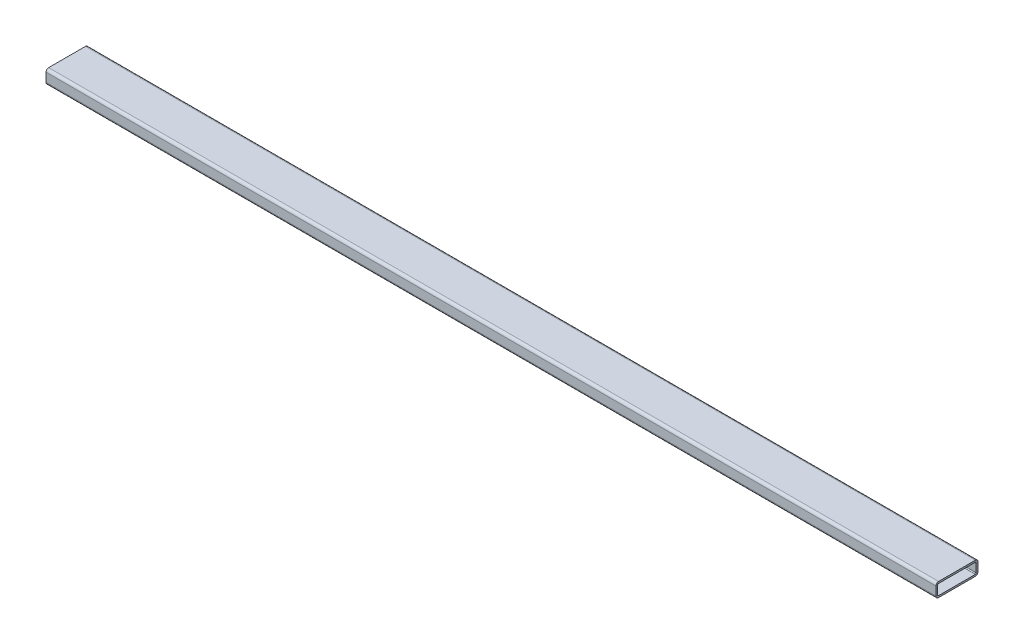
SolidWorks part; units mm, degrees
ref_plane "Front Plane" through (0, 0, 0) normal (0, 0, 1) x (1, 0, 0)
ref_plane "Top Plane" through (0, 0, 0) normal (0, 1, 0) x (1, 0, 0)
ref_plane "Right Plane" through (0, 0, 0) normal (1, 0, 0) x (0, 0, -1)
sketch "Sketch1" plane through (0, 0, 0) normal (1, 0, 0) x (0, 0, -1)
  line L0 (33.3248, 22.225) -> (-33.3248, 22.225)
  line L1 (33.3248, 25.4) -> (-33.3248, 25.4)
  line L2 (38.1, 20.6248) -> (38.1, 4.7752)
  line L3 (33.3248, 0) -> (-33.3248, 0)
  line L4 (-38.1, 20.6248) -> (-38.1, 4.7752)
  line L5 (-34.925, 20.6248) -> (-34.925, 4.7752)
  line L6 (33.3248, 3.175) -> (-33.3248, 3.175)
  line L7 (34.925, 20.6248) -> (34.925, 4.7752)
  arc A0 (38.1, 20.6248) -> (33.3248, 25.4) centre (33.3248, 20.6248) ccw
  arc A1 (38.1, 4.7752) -> (33.3248, 0) centre (33.3248, 4.7752) cw
  arc A2 (-33.3248, 0) -> (-38.1, 4.7752) centre (-33.3248, 4.7752) cw
  arc A3 (-38.1, 20.6248) -> (-33.3248, 25.4) centre (-33.3248, 20.6248) cw
  arc A4 (-34.925, 20.6248) -> (-33.3248, 22.225) centre (-33.3248, 20.6248) cw
  arc A5 (-33.3248, 3.175) -> (-34.925, 4.7752) centre (-33.3248, 4.7752) cw
  arc A6 (34.925, 4.7752) -> (33.3248, 3.175) centre (33.3248, 4.7752) cw
  arc A7 (34.925, 20.6248) -> (33.3248, 22.225) centre (33.3248, 20.6248) ccw
  point P5 (0, 0)
  dimension "D1" = 4.7752
  dimension "D2" = 25.4
  dimension "D3" = 76.2
  dimension "D4" = 3.175
extrude "Boss-Extrude1" add sketch "Sketch1" along normal mid plane 1612.9
